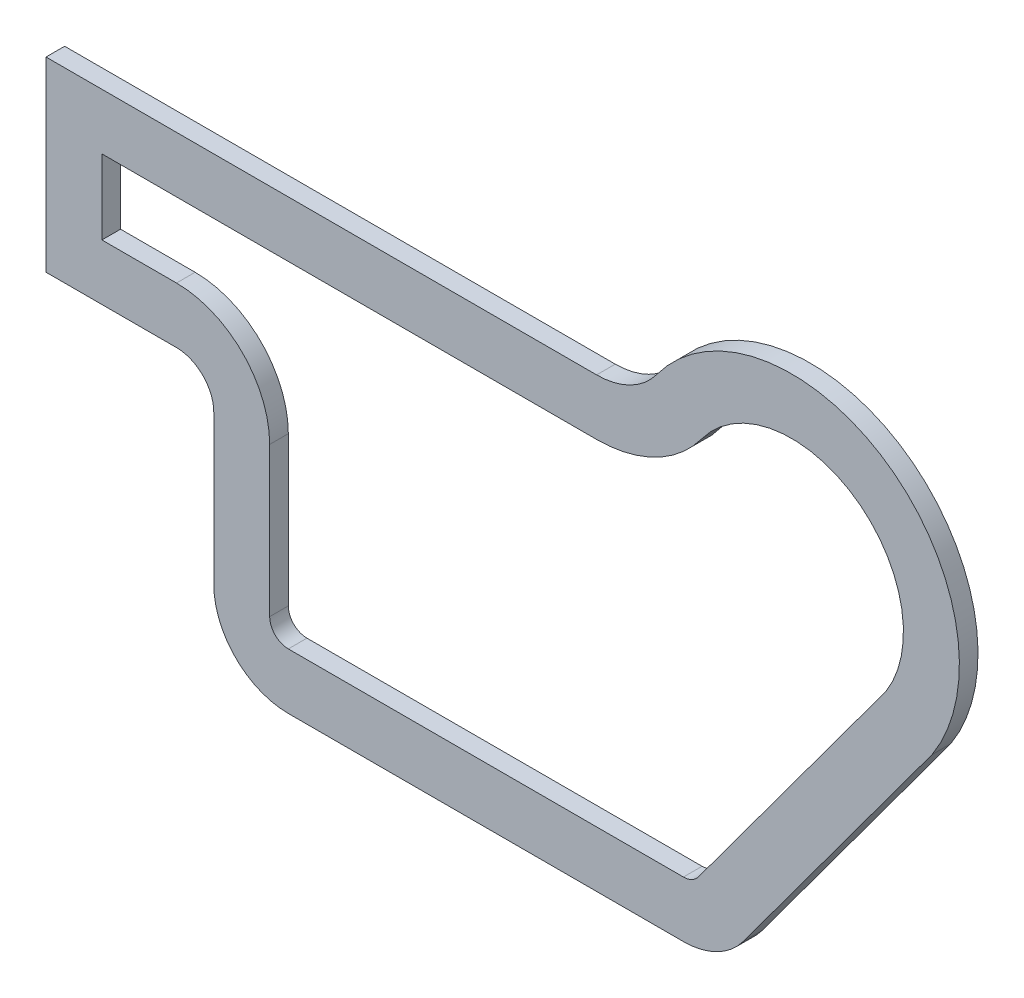
SolidWorks part; units mm, degrees
ref_plane "Front Plane" through (0, 0, 0) normal (0, 0, 1) x (1, 0, 0)
ref_plane "Top Plane" through (0, 0, 0) normal (0, 1, 0) x (1, 0, 0)
ref_plane "Right Plane" through (0, 0, 0) normal (1, 0, 0) x (0, 0, -1)
sketch "Sketch2" plane through (0, 0, 0) normal (0, 0, 1) x (1, 0, 0)
  line L0 (0, 0) -> (0, 50)
  line L2 (0, 0) -> (35, 0)
  line L5 (187.0812, -61.8638) -> (237.6661, 6.7887)
  line L7 (45, -10) -> (45, -50)
  line L8 (65, -70) -> (170.9799, -70)
  line L9 (0, 50) -> (147.6942, 50)
  line L10 (15, 35) -> (147.6942, 35)
  line L11 (175.0052, -52.966) -> (225.3156, 15.3139)
  line L12 (65, -55) -> (170.9799, -55)
  line L13 (60, -10) -> (60, -50)
  line L14 (15, 15) -> (35, 15)
  line L15 (15, 15) -> (15, 35)
  arc A1 (237.6661, 6.7887) -> (163.7883, 58.1265) centre (200, 31.4111) ccw
  arc A2 (45, -10) -> (35, 0) centre (35, -10) ccw
  arc A3 (65, -70) -> (45, -50) centre (65, -50) cw
  arc A4 (170.9799, -70) -> (187.0812, -61.8638) centre (170.9799, -50) ccw
  arc A5 (163.7883, 58.1265) -> (147.6942, 50) centre (147.6942, 70) cw
  arc A6 (175.8588, 49.2214) -> (147.6942, 35) centre (147.6942, 70) cw
  arc A7 (225.3156, 15.3139) -> (175.8588, 49.2214) centre (200, 31.4111) ccw
  arc A8 (170.9799, -55) -> (175.0052, -52.966) centre (170.9799, -50) ccw
  arc A9 (65, -55) -> (60, -50) centre (65, -50) cw
  arc A10 (60, -10) -> (35, 15) centre (35, -10) ccw
  point P9 (180, -67.8504)
  point P34 (0, 0)
  point P35 (233.787, 15)
  dimension "D1" = 45
  dimension "D2" = 200
  dimension "D4" = 10
  dimension "D6" = 20
  dimension "D5" = 20
  dimension "D10" = 20
  dimension "D3" = 50
  dimension "D7" = 120
  dimension "D8" = 45
  dimension "D9" = 180
  dimension "D12" = 68.6525
  dimension "D13" = 147.6942
  dimension "D11" = 15
extrude "Boss-Extrude1" add sketch "Sketch2" along normal blind 5
